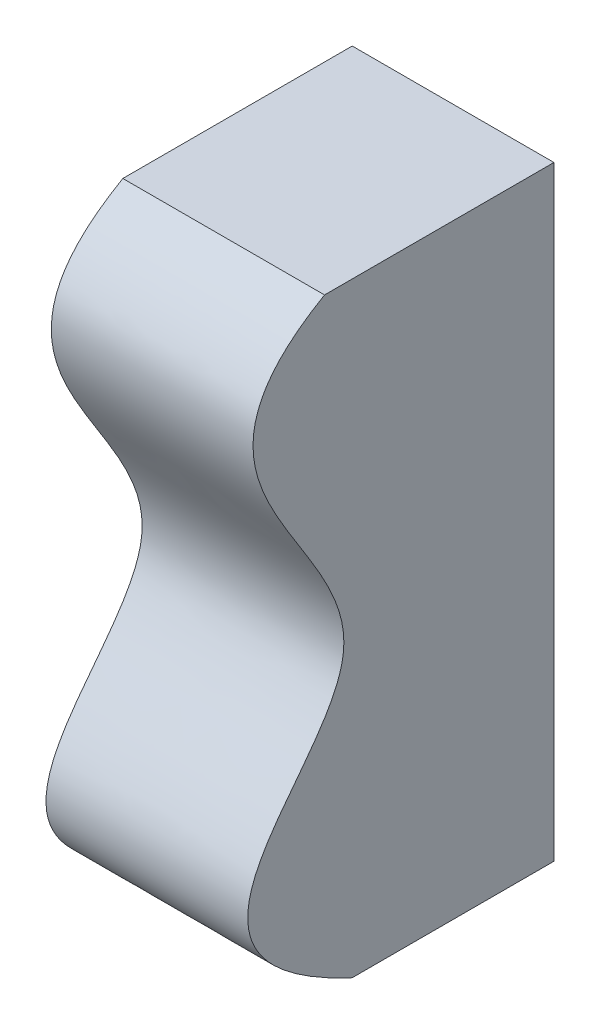
SolidWorks part; units mm, degrees
ref_plane "Front Plane" through (0, 0, 0) normal (1, 0, 0) x (0, 1, 0)
ref_plane "Top Plane" through (0, 0, 0) normal (0, 0, 1) x (0, 1, 0)
ref_plane "Right Plane" through (0, 0, 0) normal (0, 1, 0) x (-1, 0, 0)
sketch "Sketch1" plane through (0, 0, 0) normal (1, 0, 0) x (0, 1, 0)
  line L0 (0, 0) -> (0, -2.54)
  line L1 (0, -2.54) -> (7.62, -2.54)
  line L2 (7.62, -2.54) -> (7.62, 0.3487)
  spline S0 degree 3 poles (0, 0) (1.3087, 2.812) (3.5499, -2.4853) (6.3349, 2.5764) (7.62, 0.3487) knots 0 0 0 0 0.48079 1 1 1 1
  dimension "D1" = 7.62
  dimension "D2" = 2.54
extrude "Boss-Extrude1" add sketch "Sketch1" along normal blind 2.54
